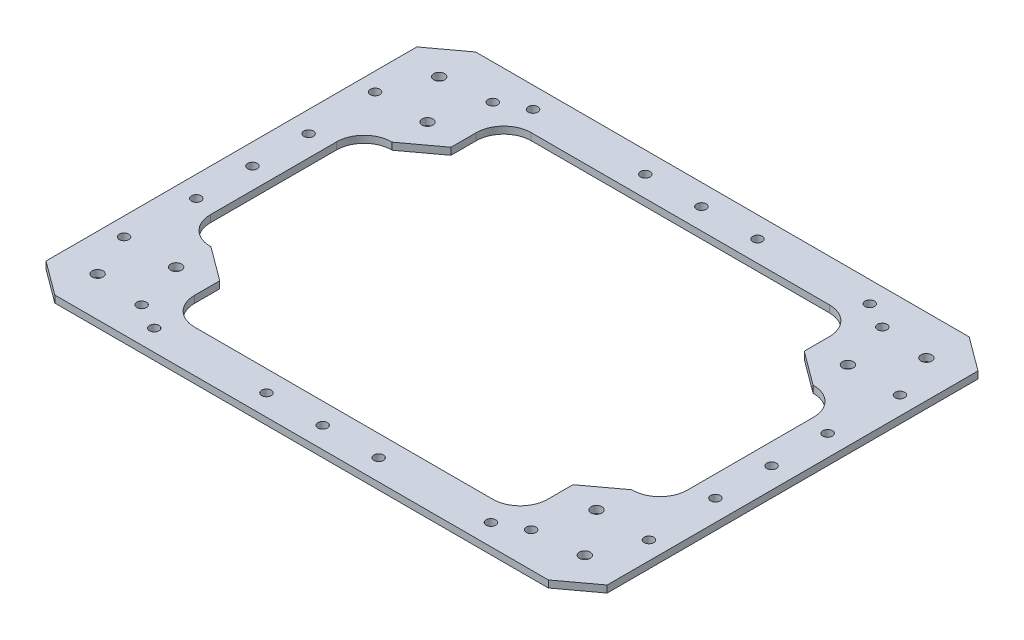
SolidWorks part; units mm, degrees
material "Thornel Mat VMA"
ref_plane "Front Plane" through (0, 0, 0) normal (0, 0, 1) x (1, 0, 0)
ref_plane "Top Plane" through (0, 0, 0) normal (0, 1, 0) x (1, 0, 0)
ref_plane "Right Plane" through (0, 0, 0) normal (1, 0, 0) x (0, 0, -1)
sketch "Sketch1" plane through (0, 0, 0) normal (0, 1, 0) x (1, 0, 0)
  line L0 (-127, 83.9186) -> (-111.6865, 95.25)
  line L1 (-127, -95.25) -> (127, -95.25)
  line L2 (-127, -95.25) -> (-127, 95.25)
  line L3 (-127, 95.25) -> (127, 95.25)
  line L4 (127, -95.25) -> (127, 95.25)
  line L5 (-107.95, 28.565) -> (-107.95, -28.565)
  line L7 (67.4905, 76.2) -> (-67.4905, 76.2)
  line L8 (-95.504, 41.011) -> (-95.25, 41.011)
  line L9 (-67.4905, -76.2) -> (67.4905, -76.2)
  line L10 (-127, 95.25) -> (127, -95.25) construction
  line L12 (127, 83.9186) -> (111.6865, 95.25)
  line L14 (79.9365, 52.3423) -> (79.9365, 63.754)
  line L15 (95.25, 41.011) -> (79.9365, 52.3423)
  line L16 (95.504, 41.011) -> (95.25, 41.011)
  line L17 (107.95, 28.565) -> (107.95, -28.565)
  line L18 (127, -83.9186) -> (111.6865, -95.25)
  line L19 (95.504, -41.011) -> (95.25, -41.011)
  line L20 (95.25, -41.011) -> (79.9365, -52.3423)
  line L21 (79.9365, -52.3423) -> (79.9365, -63.754)
  line L22 (127, 0) -> (-127, 0) construction
  line L23 (0, -13.6985) -> (0, 95.25) construction
  line L25 (-107.95, 28.565) -> (-95.504, 28.565) construction
  line L26 (-79.9365, -52.3423) -> (-79.9365, -63.754)
  line L27 (-95.25, 41.011) -> (-127, 83.9186) construction
  line L28 (-95.25, 41.011) -> (-79.9365, 52.3423)
  line L29 (-79.9365, 52.3423) -> (-79.9365, 63.754)
  line L31 (-95.25, -41.011) -> (-79.9365, -52.3423)
  line L32 (-95.504, -41.011) -> (-95.25, -41.011)
  line L33 (-127, -83.9186) -> (-111.6865, -95.25)
  line L34 (-79.9365, 52.3423) -> (-111.6865, 95.25) construction
  arc A0 (-79.9365, 63.754) -> (-67.4905, 76.2) centre (-67.4905, 63.754) cw
  arc A1 (79.9365, 63.754) -> (67.4905, 76.2) centre (67.4905, 63.754) ccw
  arc A2 (79.9365, -63.754) -> (67.4905, -76.2) centre (67.4905, -63.754) cw
  arc A3 (-67.4905, -76.2) -> (-79.9365, -63.754) centre (-67.4905, -63.754) cw
  arc A4 (-95.504, -41.011) -> (-107.95, -28.565) centre (-95.504, -28.565) cw
  arc A5 (-107.95, 28.565) -> (-95.504, 41.011) centre (-95.504, 28.565) cw
  arc A6 (95.504, 41.011) -> (107.95, 28.565) centre (95.504, 28.565) cw
  arc A7 (95.504, -41.011) -> (107.95, -28.565) centre (95.504, -28.565) ccw
  point P0 (0, 0)
  point P1 (0, 0)
  point P7 (0, -95.25)
  point P14 (0, 0)
  point P22 (0, 76.2)
  point P33 (107.95, 0)
  point P41 (0, 0)
  point P44 (-107.95, 0)
  point P45 (-38.1, 0)
  point P46 (-31.75, 0)
  dimension "D10" = 12.446
  dimension "D1" = 190.5
  dimension "D2" = 254
  dimension "D3" = 19.05
  dimension "D4" = 19.05
  dimension "D9" = 76.2
  dimension "D5" = 53.5
  dimension "D6" = 19.05
  dimension "D8" = 79.9365
extrude "Boss-Extrude1" add sketch "Sketch1" along normal blind 3.175
sketch "Sketch2" plane through (0, 3.175, 0) normal (0, 1, 0) x (1, 0, 0)
  line L0 (-87.5933, 46.6767) -> (-119.3433, 89.5843) construction
  line L1 (-95.25, 41.011) -> (-79.9365, 52.3423) construction
  line L2 (-127, 83.9186) -> (-111.6865, 95.25) construction
  line L3 (0, 0) -> (0, 95.25) construction
  line L4 (-111.6865, 95.25) -> (111.6865, 95.25) construction
  line L5 (0, 0) -> (-127, 0) construction
  line L6 (-127, -83.9186) -> (-127, 83.9186) construction
  line L7 (-103.4683, 68.1305) -> (-88.1548, 79.4619) construction
  circle A0 centre (-95.1475, 56.8856) radius 2.4638
  circle A1 centre (-110.256, 77.3036) radius 2.4638
  circle A2 centre (110.256, 77.3036) radius 2.4638
  circle A3 centre (95.1475, 56.8856) radius 2.4638
  circle A4 centre (110.256, -77.3036) radius 2.4638
  circle A5 centre (95.1475, -56.8856) radius 2.4638
  circle A6 centre (-110.256, -77.3036) radius 2.4638
  circle A7 centre (-95.1475, -56.8856) radius 2.4638
  circle A8 centre (-88.1548, 79.4619) radius 2.159
  circle A9 centre (-118.7817, 56.7991) radius 2.159
  circle A10 centre (118.7817, 56.7991) radius 2.159
  circle A11 centre (88.1548, 79.4619) radius 2.159
  circle A12 centre (118.7817, -56.7991) radius 2.159
  circle A13 centre (88.1548, -79.4619) radius 2.159
  circle A14 centre (-88.1548, -79.4619) radius 2.159
  circle A15 centre (-118.7817, -56.7991) radius 2.159
  dimension "D2" = 4.9276
  dimension "D3" = 4.9276
  dimension "D5" = 4.318
  dimension "D1" = 25.4
  dimension "D4" = 12.7
  dimension "D6" = 19.05
extrude "Cut-Extrude1" cut sketch "Sketch2" against normal through all
sketch "Sketch3" plane through (0, 3.175, 0) normal (0, 1, 0) x (1, 0, 0)
  line L0 (-79.9365, 76.2) -> (-79.9365, 95.25) construction
  line L1 (-111.6865, 95.25) -> (111.6865, 95.25) construction
  line L2 (-79.9365, 85.725) -> (79.9365, 85.725) construction
  line L3 (79.9365, 76.2) -> (79.9365, 95.25) construction
  line L4 (0, 0) -> (76.2, 0) construction
  line L5 (-107.95, -41.011) -> (-127, -41.011) construction
  line L6 (-127, -83.9186) -> (-127, 83.9186) construction
  line L7 (-107.95, 41.011) -> (-127, 41.011) construction
  line L8 (-117.475, 41.011) -> (-117.475, -41.011) construction
  line L9 (0, 0) -> (0, 36.2879) construction
  line L11 (127, -83.9186) -> (127, 83.9186) construction
  circle A0 centre (-76.2, 85.725) radius 2.159
  circle A1 centre (-25.4, 85.725) radius 2.159
  circle A2 centre (25.4, 85.725) radius 2.159
  circle A3 centre (76.2, 85.725) radius 2.159
  circle A4 centre (76.2, -85.725) radius 2.159
  circle A5 centre (25.4, -85.725) radius 2.159
  circle A6 centre (-25.4, -85.725) radius 2.159
  circle A7 centre (-76.2, -85.725) radius 2.159
  circle A8 centre (-117.475, -25.4) radius 2.159
  circle A9 centre (-117.475, 25.4) radius 2.159
  circle A10 centre (117.475, 25.4) radius 2.159
  circle A11 centre (117.475, -25.4) radius 2.159
  circle A12 centre (0, 85.725) radius 2.159
  circle A13 centre (0, -85.725) radius 2.159
  circle A14 centre (-117.475, 0) radius 2.159
  circle A15 centre (117.475, 0) radius 2.159
  point P12 (0, 85.725)
  point P40 (-117.475, 0)
  dimension "D1" = 4.318
  dimension "D2" = 76.2
  dimension "D4" = 4.318
  dimension "D5" = 25.4
  dimension "D7" = 85.725
  dimension "D8" = 127
  dimension "D9" = 127
  dimension "D3" = 4
  dimension "D6" = 2
extrude "Cut-Extrude2" cut sketch "Sketch3" against normal through all
sketch "Sketch4" plane through (0, 3.175, 0) normal (0, 1, 0) x (1, 0, 0)
  line L0 (-95.1475, -56.8856) -> (-110.256, -74.8398) construction
